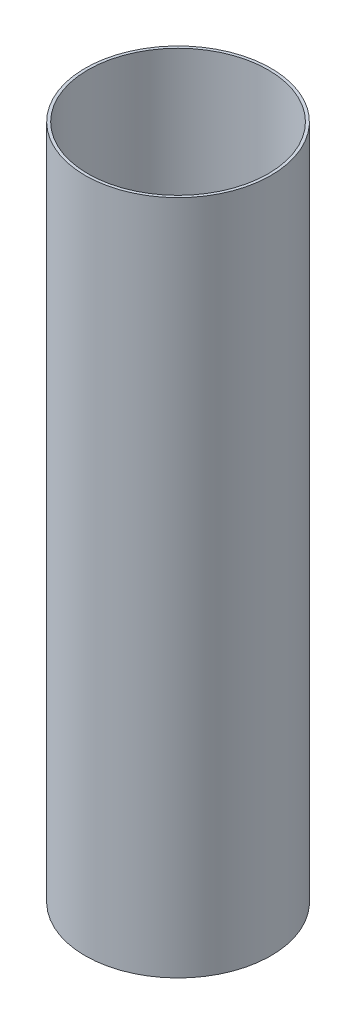
SolidWorks part; units mm, degrees
ref_plane "Front Plane" through (0, 0, 0) normal (0, 0, 1) x (1, 0, 0)
ref_plane "Top Plane" through (0, 0, 0) normal (0, 1, 0) x (1, 0, 0)
ref_plane "Right Plane" through (0, 0, 0) normal (1, 0, 0) x (0, 0, -1)
sketch "Sketch1" plane through (0, 0, 0) normal (0, 1, 0) x (1, 0, 0)
  circle A0 centre (0, 0) radius 101.6
  circle A1 centre (0, 0) radius 104.775
  dimension "D1" = 209.55
  dimension "D2" = 203.2
extrude "Boss-Extrude1" add sketch "Sketch1" along normal blind 762 contours A1 A0
